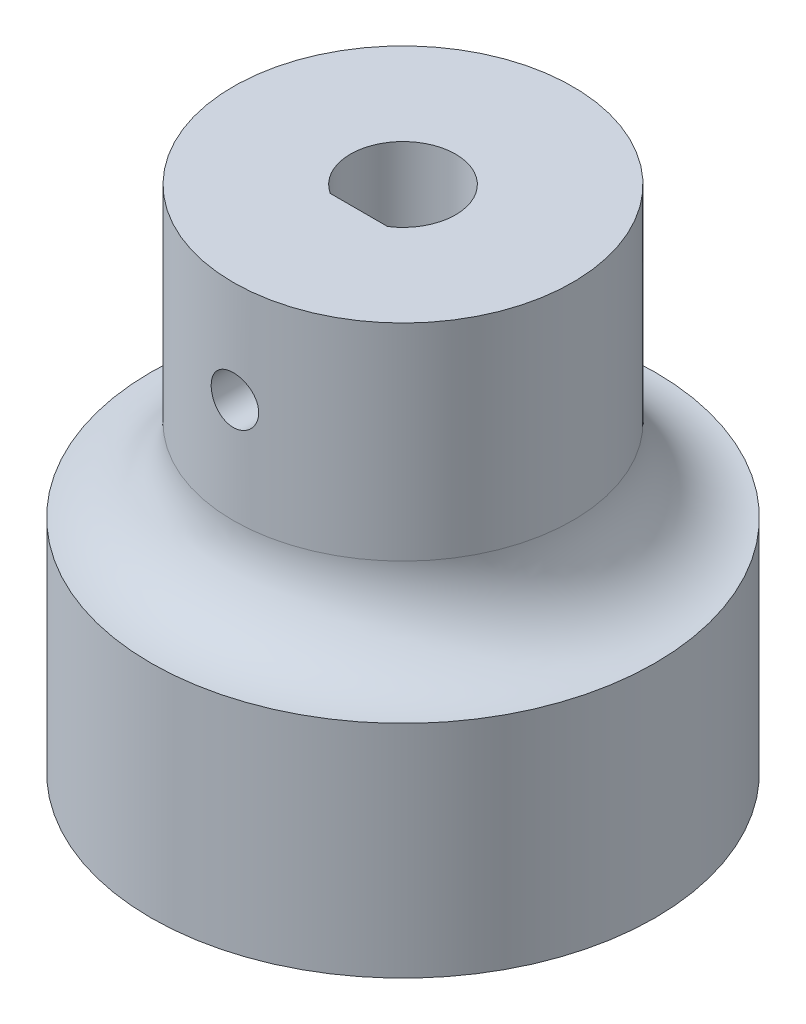
SolidWorks part; units mm, degrees
ref_plane "정면" through (0, 0, 0) normal (0, 0, 1) x (1, 0, 0)
ref_plane "윗면" through (0, 0, 0) normal (0, 1, 0) x (1, 0, 0)
ref_plane "우측면" through (0, 0, 0) normal (1, 0, 0) x (0, 0, -1)
sketch "스케치1" plane through (0, 0, 0) normal (0, 1, 0) x (1, 0, 0)
  circle A3 centre (0, 0) radius 14.85
  dimension "D2" = 29.7
extrude "보스-돌출1" add sketch "스케치1" along normal blind 13
sketch "스케치2" plane through (0, 13, 0) normal (0, 1, 0) x (1, 0, 0)
  circle A0 centre (0, 0) radius 10
  dimension "D1" = 20
extrude "보스-돌출2" add sketch "스케치2" along normal blind 17
sketch "스케치3" plane through (0, 0, 0) normal (1, 0, 0) x (0, 0, -1)
  line L0 (0, 34.6917) -> (0, -5.5082) construction
  line L1 (-14.85, 13) -> (-10, 13)
  line L2 (-10, 13) -> (-10, 17.85)
  line L3 (-10, 30) -> (-10, 13) construction
  arc A0 (-14.85, 13) -> (-10, 17.85) centre (-14.85, 17.85) ccw
  dimension "D1" = 4.85
sketch "스케치4" plane through (0, 30, 0) normal (0, 1, 0) x (1, 0, 0)
  line L0 (-1.6882, -2.6) -> (1.6882, -2.6)
  arc A0 (1.6882, -2.6) -> (-1.6882, -2.6) centre (0, 0) ccw
  dimension "D1" = 6.2
  dimension "D2" = 2.6
extrude "컷-돌출1" cut sketch "스케치4" against normal blind 12
sketch "스케치13" plane through (0, 0, 2.6) normal (0, 0, -1) x (-1, 0, 0)
  line L0 (10, 30) -> (-10, 30) construction
  circle A0 centre (0, 24) radius 1.4
  dimension "D1" = 2.8
  dimension "D2" = 6
extrude "컷-돌출2" cut sketch "스케치13" against normal through all
revolve "회전1" add sketch "스케치3" angle 360 about L0
